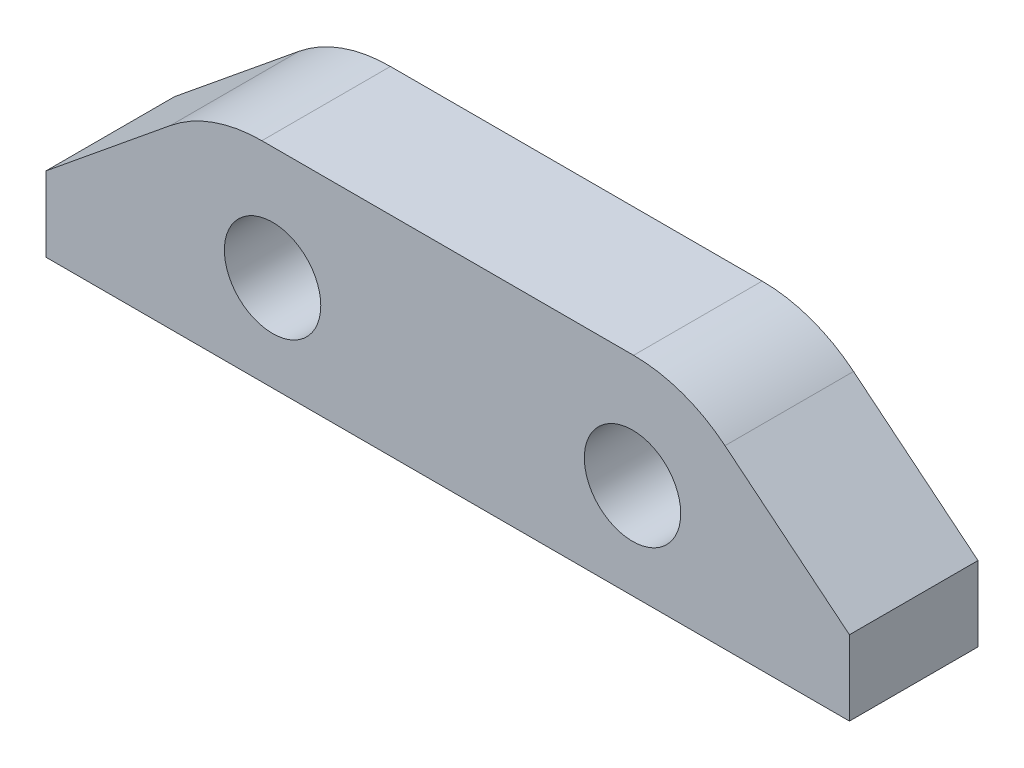
SolidWorks part; units mm, degrees
material "Beech"
ref_plane "Front Plane" through (0, 0, 0) normal (0, 0, 1) x (1, 0, 0)
ref_plane "Top Plane" through (0, 0, 0) normal (0, 1, 0) x (1, 0, 0)
ref_plane "Right Plane" through (0, 0, 0) normal (1, 0, 0) x (0, 0, -1)
sketch "Sketch1" plane through (0, 0, 0) normal (0, 0, 1) x (1, 0, 0)
  line L0 (18.2834, 6.5) -> (6.7166, 6.5)
  line L1 (25, 2.3282) -> (21.1279, 5.4869)
  line L2 (3.8721, 5.4869) -> (0, 2.3282)
  line L3 (0, 0) -> (25, 0)
  line L4 (25, 0) -> (25, 2.3282)
  line L5 (0, 0) -> (0, 2.3282)
  circle A0 centre (7.05, 2.97) radius 1.5
  circle A1 centre (18.25, 2.97) radius 1.5
  arc A2 (21.1279, 5.4869) -> (18.2834, 6.5) centre (18.2834, 2) ccw
  arc A3 (6.7166, 6.5) -> (3.8721, 5.4869) centre (6.7166, 2) ccw
extrude "Boss-Extrude1" add sketch "Sketch1" along normal blind 4
